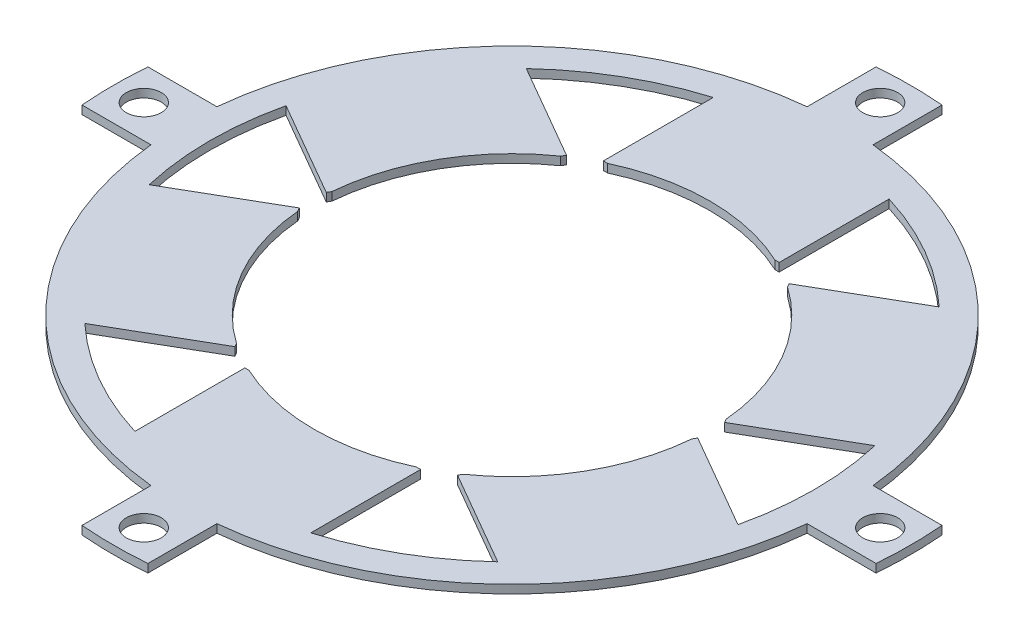
SolidWorks part; units mm, degrees
material "1023 Carbon Steel Sheet (SS)"
ref_plane "Front Plane" through (0, 0, 0) normal (0, 0, 1) x (1, 0, 0)
ref_plane "Top Plane" through (0, 0, 0) normal (0, 1, 0) x (1, 0, 0)
ref_plane "Right Plane" through (0, 0, 0) normal (1, 0, 0) x (0, 0, -1)
sketch "Sketch1" plane through (0, 0, 0) normal (0, 1, 0) x (1, 0, 0)
  line L20 (-6, 72.2513) -> (-6, 59.6992)
  line L21 (6, 72.2513) -> (6, 59.6992)
  line L26 (72.2513, 6) -> (59.6992, 6)
  line L27 (72.2513, -6) -> (59.6992, -6)
  line L28 (6, -72.2513) -> (6, -59.6992)
  line L29 (-6, -72.2513) -> (-6, -59.6992)
  line L30 (-72.2513, -6) -> (-59.6992, -6)
  line L31 (-72.2513, 6) -> (-59.6992, 6)
  line L32 (20.2509, 30.1671) -> (37.5714, 40.1671)
  line L33 (36.2509, 2.4542) -> (20.2509, 30.1671)
  line L34 (16, 32.6213) -> (-16, 32.6213)
  line L35 (16, 32.6213) -> (16, 52.6213)
  line L37 (-16, 32.6213) -> (-16, 52.6213)
  line L38 (16, 32.6213) -> (-16, 52.6213) construction
  line L39 (16, 52.6213) -> (-16, 32.6213) construction
  line L40 (36.2509, 2.4542) -> (53.5714, 12.4542)
  line L41 (36.2509, -2.4542) -> (53.5714, -12.4542)
  line L42 (20.2509, -30.1671) -> (36.2509, -2.4542)
  line L43 (20.2509, -30.1671) -> (37.5714, -40.1671)
  line L44 (16, -32.6213) -> (16, -52.6213)
  line L45 (-16, -32.6213) -> (16, -32.6213)
  line L46 (-16, -32.6213) -> (-16, -52.6213)
  line L47 (-20.2509, -30.1671) -> (-37.5714, -40.1671)
  line L48 (-36.2509, -2.4542) -> (-20.2509, -30.1671)
  line L49 (-36.2509, -2.4542) -> (-53.5714, -12.4542)
  line L50 (-36.2509, 2.4542) -> (-53.5714, 12.4542)
  line L51 (-20.2509, 30.1671) -> (-36.2509, 2.4542)
  line L52 (-20.2509, 30.1671) -> (-37.5714, 40.1671)
  arc A9 (6, 72.2513) -> (-6, 72.2513) centre (0, 0) ccw
  arc A10 (72.2513, -6) -> (72.2513, 6) centre (0, 0) ccw
  arc A11 (-6, -72.2513) -> (6, -72.2513) centre (0, 0) ccw
  arc A12 (-72.2513, 6) -> (-72.2513, -6) centre (0, 0) ccw
  arc A13 (-6, 59.6992) -> (-59.6992, 6) centre (0, 0) ccw
  arc A14 (59.6992, 6) -> (6, 59.6992) centre (0, 0) ccw
  arc A15 (-59.6992, -6) -> (-6, -59.6992) centre (0, 0) ccw
  arc A16 (6, -59.6992) -> (59.6992, -6) centre (0, 0) ccw
  circle A17 centre (0, 67) radius 3.175
  circle A18 centre (67, 0) radius 3.175
  circle A19 centre (0, -67) radius 3.175
  circle A20 centre (-67, 0) radius 3.175
  arc A22 (-16, 52.6213) -> (-37.5714, 40.1671) centre (0, 0) ccw
  arc A23 (-53.5714, 12.4542) -> (-53.5714, -12.4542) centre (0, 0) ccw
  arc A24 (-16, -52.6213) -> (-37.5714, -40.1671) centre (0, 0) cw
  arc A25 (16, -52.6213) -> (37.5714, -40.1671) centre (0, 0) ccw
  arc A26 (53.5714, -12.4542) -> (53.5714, 12.4542) centre (0, 0) ccw
  arc A27 (16, 52.6213) -> (37.5714, 40.1671) centre (0, 0) cw
  point P4 (0, 42.6213)
  point P6 (0, 45)
  point P32 (0, 0)
  point P52 (0, 0)
  point P56 (0, 0)
  point P59 (0, 0)
  dimension "D1" = 6.35
  dimension "D2" = 12
  dimension "D8" = 72.5
  dimension "D11" = 67
  dimension "D9" = 60
  dimension "D12" = 55
  dimension "D13" = 55
  dimension "D21" = 55
  dimension "D22" = 55
  dimension "D3" = 20
  dimension "D4" = 32
  dimension "D5" = 4
  dimension "D7" = 6
  dimension "D10" = 6
  dimension "D14" = 20
  dimension "D15" = 20
  dimension "D16" = 20
  dimension "D17" = 20
  dimension "D18" = 20
  dimension "D19" = 20
  dimension "D20" = 12.5521
  dimension "D6" = 4
sketch "Sketch3" plane through (0, 0, 0) normal (0, 1, 0) x (1, 0, 0)
  circle A0 centre (0, 0) radius 36
  dimension "D1" = 72
extrude "Boss-Extrude5" add sketch "Sketch1" along normal blind 1.52
extrude "Cut-Extrude4" cut sketch "Sketch3" along normal through all
